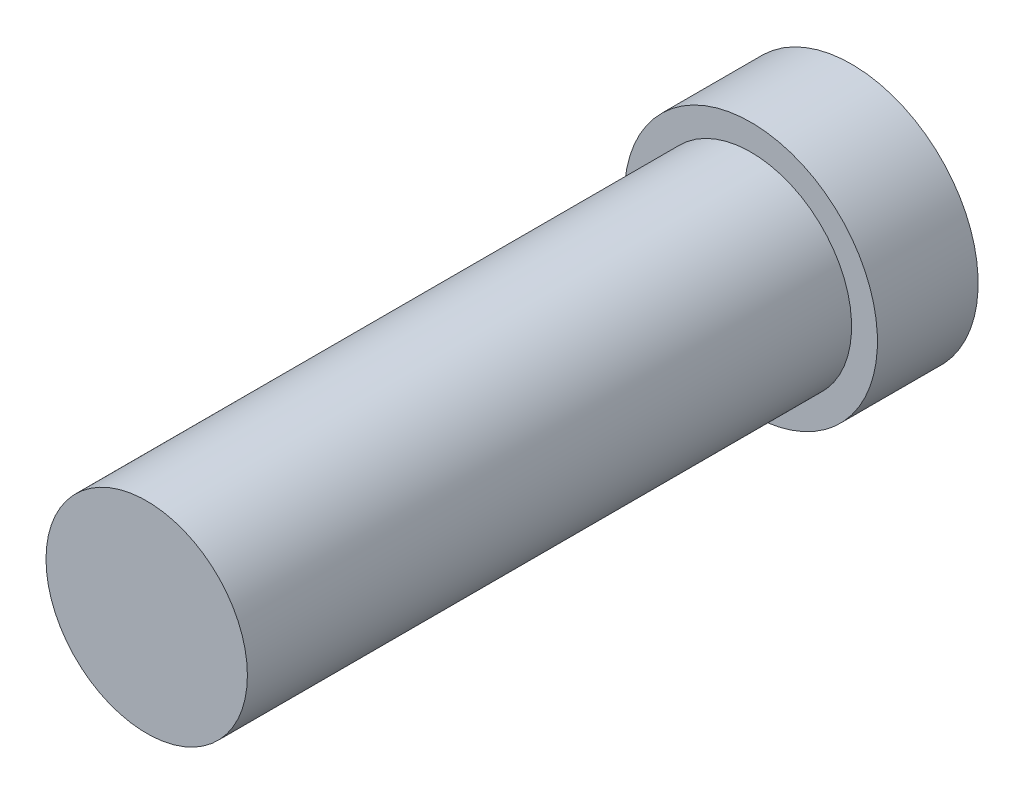
SolidWorks part; units mm, degrees
ref_plane "Front Plane" through (0, 0, 0) normal (0, 0, 1) x (1, 0, 0)
ref_plane "Top Plane" through (0, 0, 0) normal (0, 1, 0) x (1, 0, 0)
ref_plane "Right Plane" through (0, 0, 0) normal (1, 0, 0) x (0, 0, -1)
sketch "Sketch1" plane through (0, 0, 0) normal (0, 0, 1) x (1, 0, 0)
  circle A0 centre (0, 0) radius 3
extrude "Boss-Extrude1" add sketch "Sketch1" along normal blind 20
sketch "Sketch2" plane through (0, 0, 0) normal (0, 0, -1) x (-1, 0, 0)
  circle A0 centre (0, 0) radius 2.7701
extrude "Extrude-Thin1" add sketch "Sketch2" against normal blind 2 and the other way blind 1 thin
